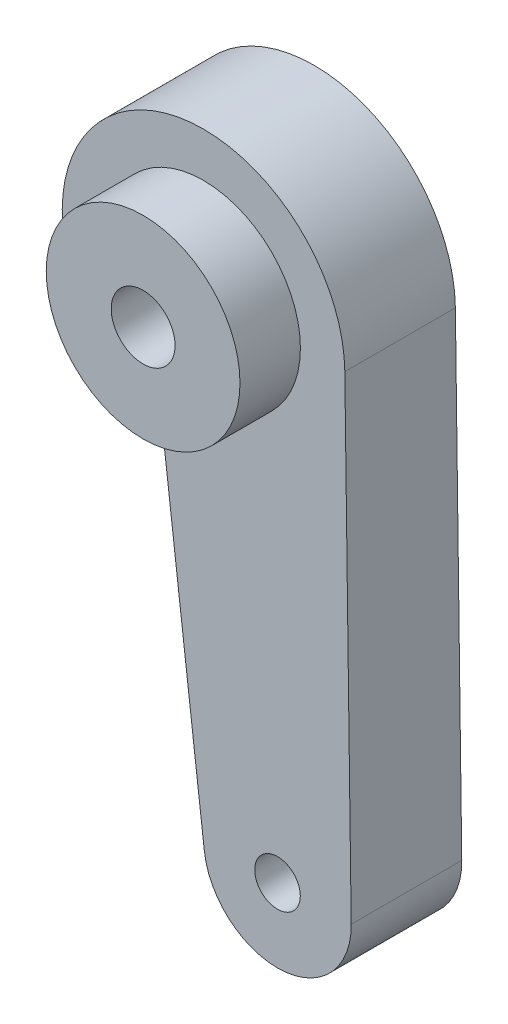
SolidWorks part; units mm, degrees
ref_plane "Plano frontal" through (0, 0, 0) normal (0, 0, 1) x (1, 0, 0)
ref_plane "Plano superior" through (0, 0, 0) normal (0, 1, 0) x (1, 0, 0)
ref_plane "Plano direito" through (0, 0, 0) normal (1, 0, 0) x (0, 0, -1)
sketch "Esboço1" plane through (0, 0, 0) normal (0, 0, 1) x (1, 0, 0)
  line L0 (-3.6315, -11.8554) -> (0.0719, -42.4123)
  line L1 (12.398, 0.1664) -> (12.9578, -41.5475)
  arc A2 (12.398, 0.1664) -> (-3.6315, -11.8554) centre (0, 0) ccw
  circle A3 centre (6.4917, -41.6343) radius 2
  arc A4 (0.0719, -42.4123) -> (12.9578, -41.5475) centre (6.4917, -41.6343) ccw
  circle A5 centre (0, 0) radius 5.5
extrude "Ressalto-extrusão1" add sketch "Esboço1" along normal blind 9.7
sketch "Esboço2" plane through (0, 0, 9.7) normal (0, 0, 1) x (1, 0, 0)
  circle A0 centre (0, 0) radius 2.8
  circle A1 centre (0, 0) radius 8.5
extrude "Ressalto-extrusão2" add sketch "Esboço2" along normal blind 5.3
